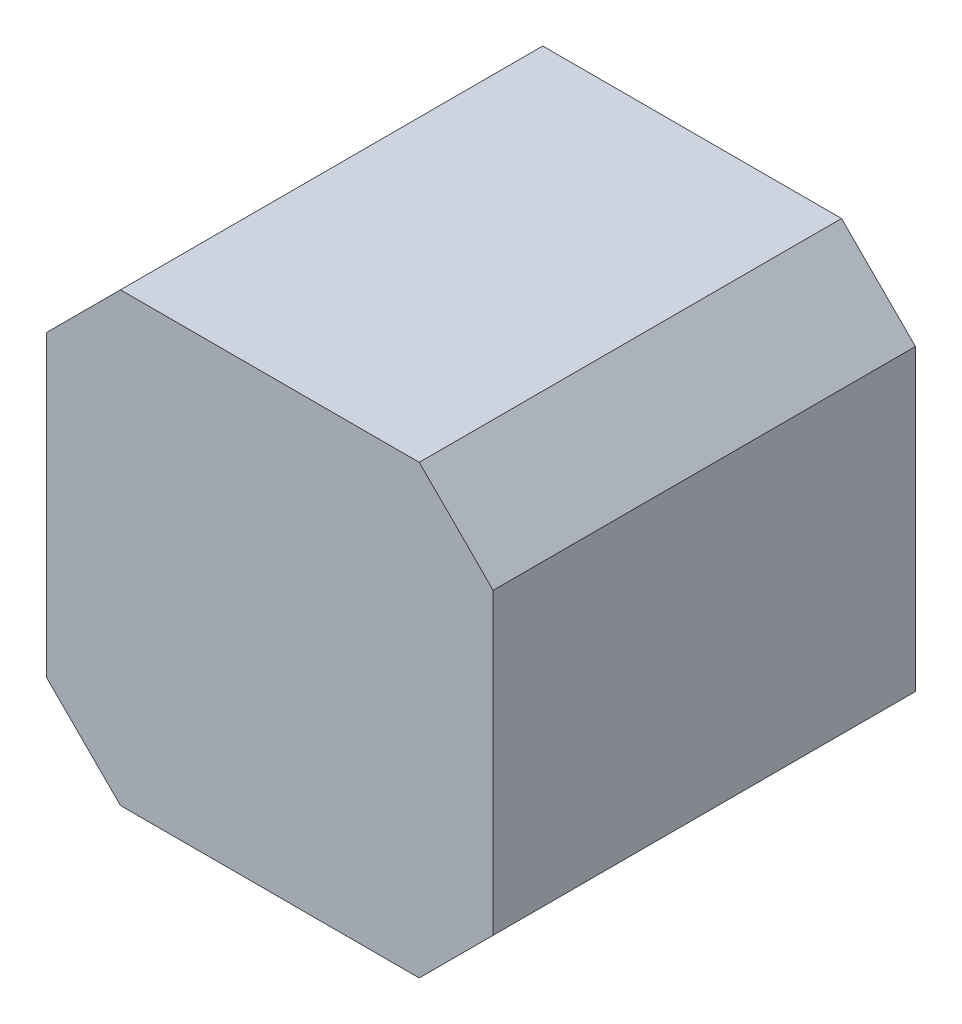
SolidWorks part; units mm, degrees
material "Acero aleado"
ref_plane "Plane1" through (0, 0, 0) normal (0, 0, 1) x (1, 0, 0)
ref_plane "Plane2" through (0, 0, 0) normal (0, 1, 0) x (1, 0, 0)
ref_plane "Plane3" through (0, 0, 0) normal (1, 0, 0) x (0, 0, -1)
sketch "Sketch1" plane through (0, 0, 0) normal (0, 0, 1) x (1, 0, 0)
  line L0 (-14.15, 21.15) -> (-21.15, 14.15)
  line L1 (-14.15, 21.15) -> (14.15, 21.15)
  line L2 (-21.15, 14.15) -> (-21.15, -14.15)
  line L3 (-14.15, -21.15) -> (14.15, -21.15)
  line L4 (21.15, 14.15) -> (21.15, -14.15)
  line L5 (-21.15, 21.15) -> (21.15, -21.15) construction
  line L6 (-21.15, -21.15) -> (21.15, 21.15) construction
  line L7 (14.15, 21.15) -> (21.15, 14.15)
  line L8 (21.15, -14.15) -> (14.15, -21.15)
  line L9 (-21.15, -14.15) -> (-14.15, -21.15)
  point P0 (0, 0)
  dimension "D1" = 42.3
  dimension "D2" = 42.3
extrude "Extrude1" add sketch "Sketch1" along normal blind 40
